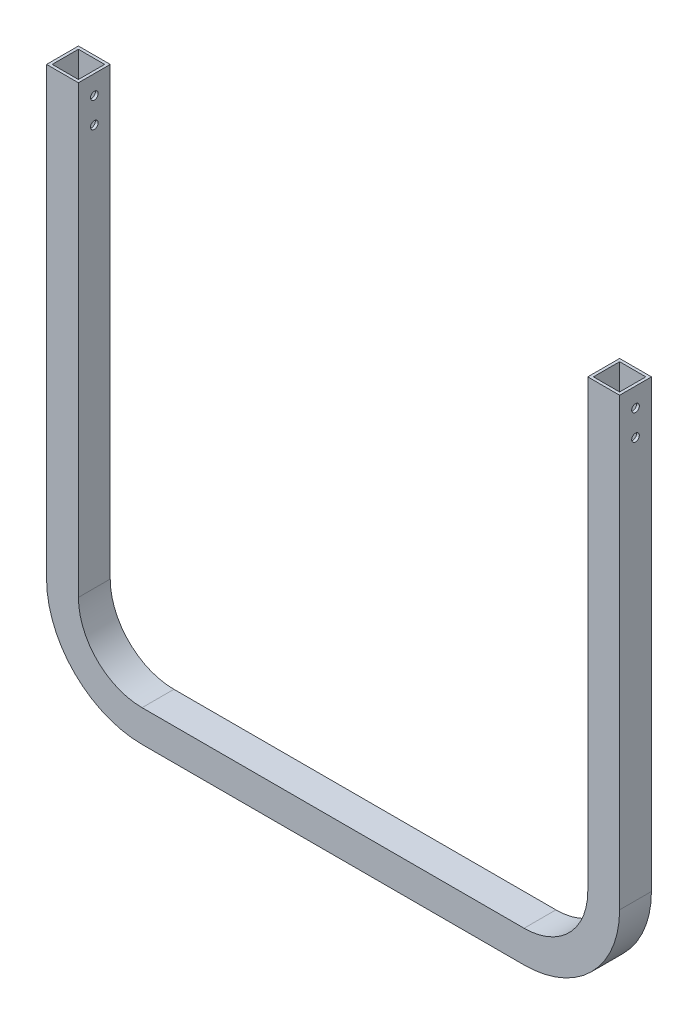
SolidWorks part; units mm, degrees
ref_plane "Спереди" through (0, 0, 0) normal (0, 0, 1) x (1, 0, 0)
ref_plane "Сверху" through (0, 0, 0) normal (0, 1, 0) x (1, 0, 0)
ref_plane "Справа" through (0, 0, 0) normal (1, 0, 0) x (0, 0, -1)
sketch "Эскиз1" plane through (0, 0, 0) normal (0, 0, 1) x (1, 0, 0)
  line L0 (-260.936, 123.1156) -> (-260.936, -226.8844)
  line L2 (-235.936, 123.1156) -> (-235.936, -226.8844)
  line L3 (-185.936, -276.8844) -> (114.064, -276.8844)
  line L4 (164.064, 123.1156) -> (164.064, -226.8844)
  line L5 (-185.936, -301.8844) -> (114.064, -301.8844)
  line L6 (189.064, 123.1156) -> (189.064, -226.8844)
  line L7 (-260.936, 123.1156) -> (-235.936, 123.1156)
  line L8 (164.064, 123.1156) -> (189.064, 123.1156)
  arc A0 (114.064, -276.8844) -> (164.064, -226.8844) centre (114.064, -226.8844) ccw
  arc A1 (-235.936, -226.8844) -> (-185.936, -276.8844) centre (-185.936, -226.8844) ccw
  arc A2 (-260.936, -226.8844) -> (-185.936, -301.8844) centre (-185.936, -226.8844) ccw
  arc A3 (114.064, -301.8844) -> (189.064, -226.8844) centre (114.064, -226.8844) ccw
  point P8 (-235.936, -276.8844)
  dimension "D3" = 50
  dimension "D1" = 400
  dimension "D2" = 400
  dimension "D4" = 25
extrude "Бобышка-Вытянуть1" add sketch "Эскиз1" along normal blind 25
shell "Оболочка1" thickness 2.2
sketch "Эскиз2" plane through (0, 123.1156, 0) normal (0, 1, 0) x (1, 0, 0)
  line L6 (166.264, -2.2) -> (166.264, -22.8)
  line L7 (166.264, -22.8) -> (186.864, -22.8)
  line L8 (186.864, -2.2) -> (186.864, -22.8)
  line L9 (166.264, -2.2) -> (186.864, -2.2)
extrude "Вырез-Вытянуть1" cut sketch "Эскиз2" against normal blind 5
sketch "Эскиз3" plane through (-260.936, 0, 0) normal (-1, 0, 0) x (0, 0, 1)
  line L0 (12.5, 123.1156) -> (12.5, 41.236) construction
  line L1 (25, 123.1156) -> (0, 123.1156) construction
  circle A0 centre (12.5, 108.1156) radius 3
  circle A1 centre (12.5, 88.1156) radius 3
  dimension "D1" = 15
  dimension "D2" = 20
extrude "Вырез-Вытянуть2" cut sketch "Эскиз3" against normal through all
